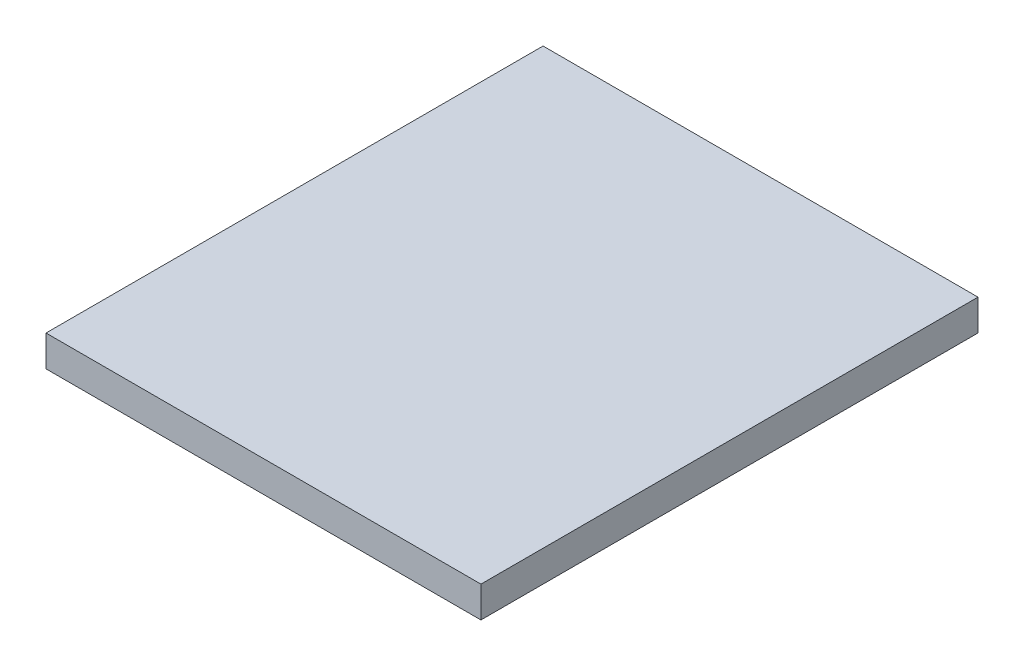
SolidWorks part; units mm, degrees
ref_plane "Front Plane" through (0, 0, 0) normal (0, 0, 1) x (1, 0, 0)
ref_plane "Top Plane" through (0, 0, 0) normal (0, 1, 0) x (1, 0, 0)
ref_plane "Right Plane" through (0, 0, 0) normal (1, 0, 0) x (0, 0, -1)
sketch "Sketch1" plane through (0, 0, 0) normal (0, 1, 0) x (1, 0, 0)
  line L0 (-355.6, 406.4) -> (355.6, -406.4) construction
  line L1 (-355.6, 406.4) -> (355.6, 406.4)
  line L2 (-355.6, 406.4) -> (-355.6, -406.4)
  line L3 (-355.6, -406.4) -> (355.6, -406.4)
  line L4 (355.6, 406.4) -> (355.6, -406.4)
  dimension "D1" = 711.2
  dimension "D2" = 812.8
extrude "Boss-Extrude1" add sketch "Sketch1" along normal mid plane 50.8
